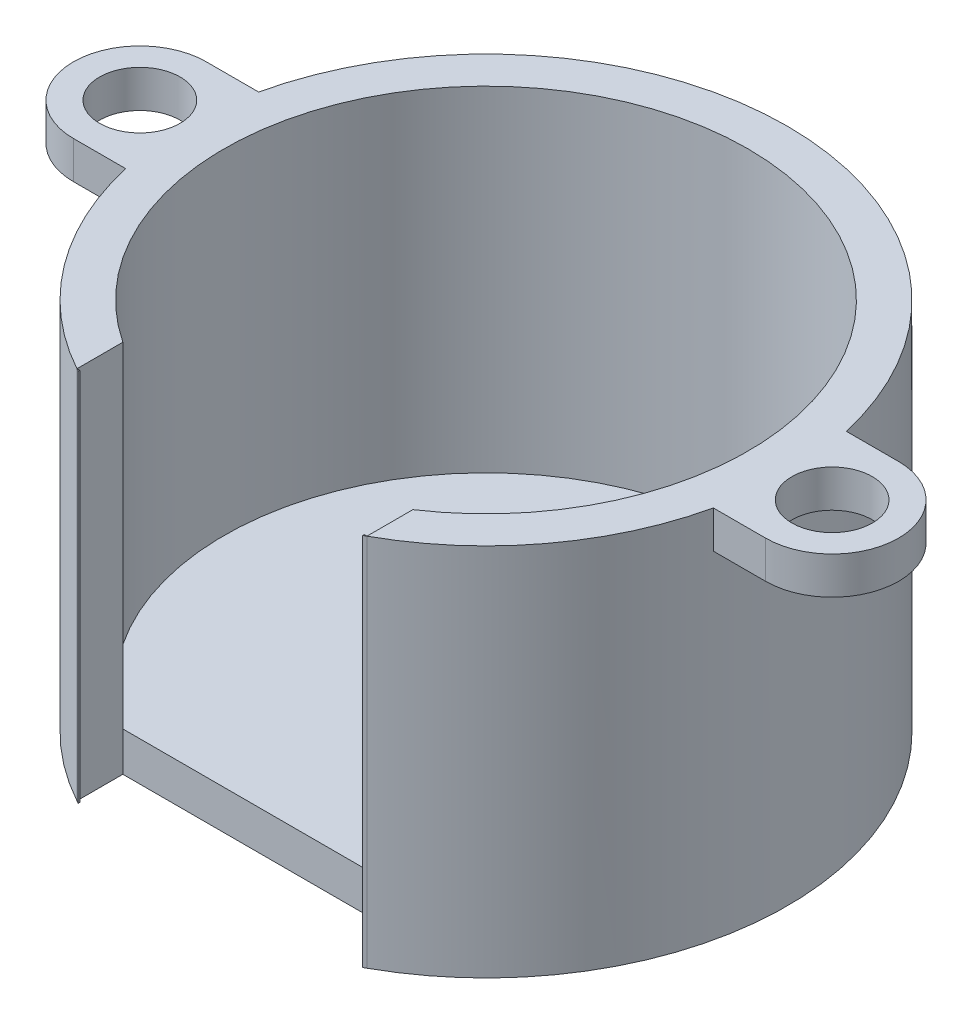
SolidWorks part; units mm, degrees
ref_plane "Front Plane" through (0, 0, 0) normal (0, 0, 1) x (1, 0, 0)
ref_plane "Top Plane" through (0, 0, 0) normal (0, 1, 0) x (1, 0, 0)
ref_plane "Right Plane" through (0, 0, 0) normal (1, 0, 0) x (0, 0, -1)
sketch "Sketch1" plane through (0, 0, 0) normal (0, 1, 0) x (1, 0, 0)
  line L1 (-7.6, -14.1933) -> (7.6, -14.1933)
  line L5 (-7.6, -14.1933) -> (7.6, 14.1933) construction
  line L6 (-7.074, 13.2111) -> (7.6, -14.1933) construction
  arc A0 (7.6, -14.1933) -> (-7.6, -14.1933) centre (0, 0) ccw
  dimension "D1" = 32.2
  dimension "D2" = 15.2
extrude "Boss-Extrude1" add sketch "Sketch1" along normal blind 20
shell "Shell2" thickness 2.1
sketch "Sketch2" plane through (0, 20, 0) normal (0, 1, 0) x (1, 0, 0)
  line L0 (-18.5, 3.55) -> (-15.7037, 3.55)
  line L2 (-18.5, -3.55) -> (-15.7037, -3.55)
  line L3 (0, -11) -> (0, 11) construction
  line L4 (18.5, -3.55) -> (15.7037, -3.55)
  line L5 (18.5, 3.55) -> (15.7037, 3.55)
  circle A0 centre (0, 0) radius 14 construction
  circle A1 centre (0, 0) radius 16.1 construction
  circle A2 centre (0, 0) radius 14
  circle A3 centre (0, 0) radius 16.1
  circle A4 centre (-18.5, 0) radius 2.15
  circle A5 centre (18.5, 0) radius 2.15
  arc A6 (-18.5, 3.55) -> (-18.5, -3.55) centre (-18.5, 0) ccw
  arc A7 (18.5, 3.55) -> (18.5, -3.55) centre (18.5, 0) cw
  dimension "D5" = 4.3
  dimension "D6" = 4.3
  dimension "D4" = 7.1
  dimension "D2" = 18.5
  dimension "D1" = 37
extrude "Boss-Extrude2" add sketch "Sketch2" against normal blind 2
sketch "Sketch3" plane through (0, 20, 0) normal (0, 1, 0) x (1, 0, 0)
  line L1 (-7.75, -14.112) -> (7.75, -14.112)
  line L2 (-7.75, -14.112) -> (-7.75, -11.6592)
  line L4 (7.75, -14.112) -> (7.75, -11.6592)
  line L5 (-7.75, -11.6592) -> (7.75, -11.6592)
  circle A0 centre (0, 0) radius 16.1 construction
  circle A1 centre (0, 0) radius 14 construction
  circle A2 centre (0, 0) radius 14
  circle A3 centre (0, 0) radius 16.1
  point P1 (-7.6, -11.7576)
  point P2 (-8.2007, -14.3503)
  point P6 (-7.75, -11.9644)
  dimension "D1" = 15.5
extrude "Cut-Extrude1" cut sketch "Sketch3" against normal through all contours L5 L4 L1 L2
sketch "Sketch4" plane through (0, 0, 14.1933) normal (0, 0, 1) x (1, 0, 0)
  line L4 (-7.6, 0) -> (7.6, 0)
  line L5 (7.6, 0) -> (7.6, 20)
  line L6 (7.6, 20) -> (-7.6, 20)
  line L7 (-7.6, 20) -> (-7.6, 0)
  line L8 (-7.6, 0) -> (7.6, 0)
  line L9 (7.6, 0) -> (7.6, 20)
  line L10 (7.6, 20) -> (-7.6, 20)
  line L11 (-7.6, 20) -> (-7.6, 0)
  dimension "D1" = 0
extrude "Cut-Extrude2" cut sketch "Sketch4" against normal up to next
